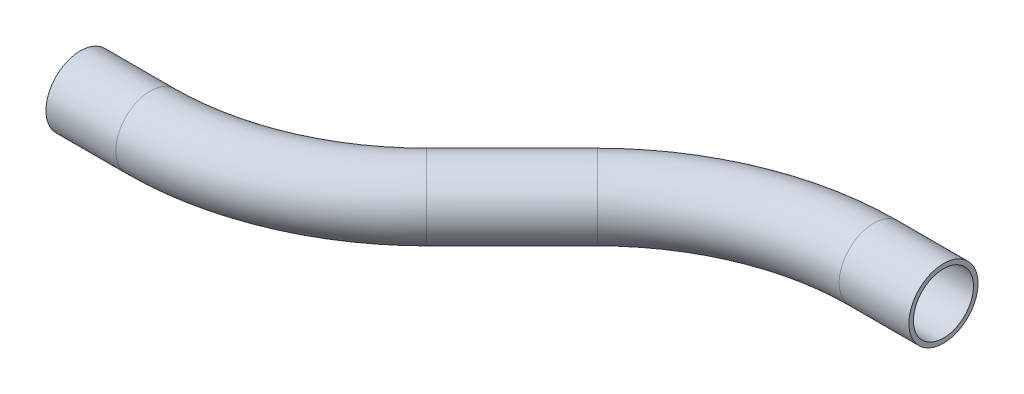
SolidWorks part; units mm, degrees
ref_plane "Front Plane" through (0, 0, 0) normal (0, 0, 1) x (1, 0, 0)
ref_plane "Top Plane" through (0, 0, 0) normal (0, 1, 0) x (1, 0, 0)
ref_plane "Right Plane" through (0, 0, 0) normal (1, 0, 0) x (0, 0, -1)
sketch "Sketch1" plane through (0, 0, 0) normal (0, 1, 0) x (1, 0, 0)
  line L0 (0, 0) -> (19.2369, 0)
  line L1 (73.1185, 22.3185) -> (96.6377, 45.8377)
  line L2 (150.5192, 68.1561) -> (169.7561, 68.1561)
  arc A0 (96.6377, 45.8377) -> (150.5192, 68.1561) centre (150.5192, -8.0439) cw
  arc A1 (19.2369, 0) -> (73.1185, 22.3185) centre (19.2369, 76.2) ccw
  point P7 (118.9561, 68.1561)
  point P10 (50.8, 0)
  dimension "D5" = 76.2
  dimension "D1" = 50.8
  dimension "D2" = 50.8
  dimension "D3" = 135
  dimension "D4" = 68.1561
ref_plane "Plane1" through (0, 0, 0) normal (1, 0, 0) x (0, 0, -1)
sketch "Sketch2" plane through (0, 0, 0) normal (1, 0, 0) x (0, 0, -1)
  circle A0 centre (0, 0) radius 9.525
  circle A1 centre (0, 0) radius 8.2804
  dimension "D1" = 19.05
  dimension "D2" = 1.2446
sweep "Sweep1" add profiles "Sketch2" path "Sketch1"
